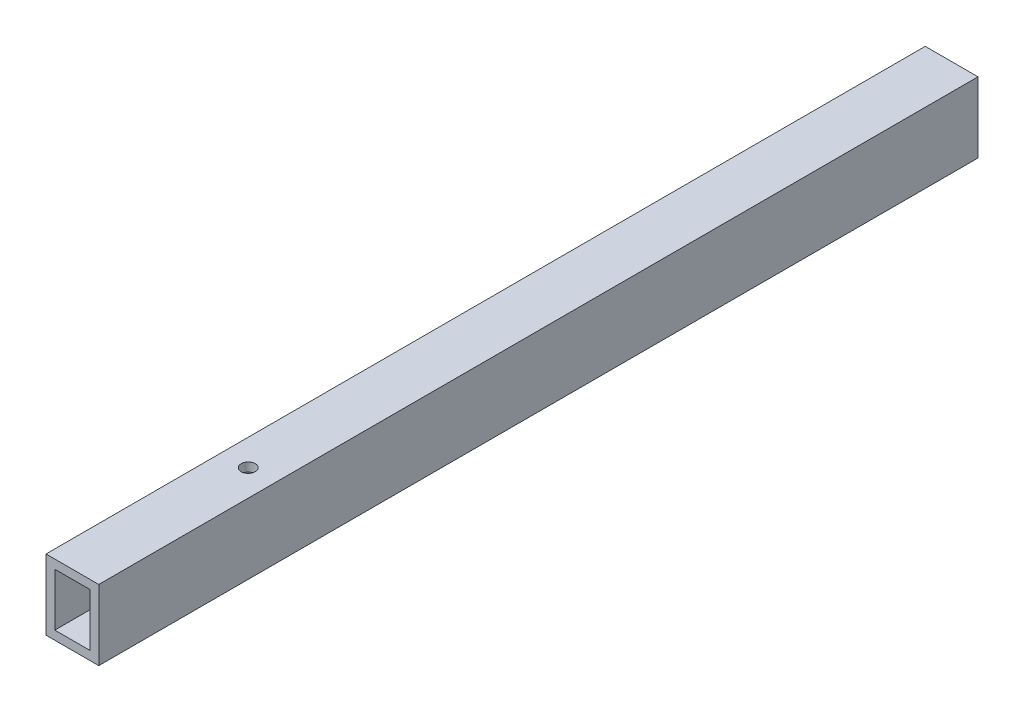
SolidWorks part; units mm, degrees
ref_plane "Plan de face" through (0, 0, 0) normal (0, 0, 1) x (1, 0, 0)
ref_plane "Plan de dessus" through (0, 0, 0) normal (0, 1, 0) x (1, 0, 0)
ref_plane "Plan de droite" through (0, 0, 0) normal (1, 0, 0) x (0, 0, -1)
sketch "Esquisse1" plane through (0, 0, 0) normal (0, 0, 1) x (1, 0, 0)
  line L1 (0, 0) -> (6, 0)
  line L2 (0, 0) -> (0, 8)
  line L3 (0, 8) -> (6, 8)
  line L4 (6, 0) -> (6, 8)
  dimension "D1" = 6
  dimension "D2" = 8
extrude "Boss.-Extru.1" add sketch "Esquisse1" against normal blind 100
sketch "Esquisse2" plane through (0, 0, 0) normal (0, 0, 1) x (1, 0, 0)
  line L0 (6, 0) -> (6, 8) construction
  line L1 (1, 7) -> (5, 7)
  line L2 (1, 7) -> (1, 1)
  line L3 (1, 1) -> (5, 1)
  line L4 (5, 7) -> (5, 1)
  line L5 (0, 0) -> (6, 0) construction
  dimension "D1" = 4
  dimension "D2" = 6
  dimension "D3" = 1
  dimension "D4" = 1
extrude "Enlèv. mat.-Extru.1" cut sketch "Esquisse2" against normal blind 80
hole_wizard "Trou taraudé M21" positions "Esquisse3" profile "Esquisse4" tap size "M2" standard "ISO"
sketch "Esquisse3" plane through (0, 8, 0) normal (0, 1, 0) x (1, 0, 0)
  line L0 (6, 0) -> (0, 0) construction
  line L1 (0, 100) -> (0, 0) construction
  point P0 (3, 20)
  dimension "D1" = 20
  dimension "D2" = 3
sketch "Esquisse4" plane through (3, 8, -20) normal (1, 0, 0) x (0, 0, 1)
  line L0 (0, 0) -> (0, 4.4807)
  line L1 (0, 4.4807) -> (0.8, 4)
  line L2 (0.8, 4) -> (0.8, 0)
  line L5 (0.8, 0) -> (0, 0)
  line L10 (0, 4.4807) -> (-0.8, 4) construction
  line L11 (0, -6.35) -> (0, 107.95) construction
  dimension "Diamètre du trou pour taraudage" = 1.6
  dimension "Profondeur du trou pour taraudage" = 4
  dimension "Angle de pointe" = 118
cosmetic thread "Filetage de perçage1" parameters "D1"=1, "D2"=2
hole_wizard "Trou taraudé M31" positions "Esquisse5" profile "Esquisse6" tap size "M3" standard "ISO"
sketch "Esquisse5" plane through (0, 0, -100) normal (0, 0, -1) x (-1, 0, 0)
  line L0 (0, 8) -> (0, 0) construction
  line L1 (-6, 8) -> (0, 8) construction
  point P0 (-3, 4)
  dimension "D1" = 3
  dimension "D2" = 4
cosmetic thread "Filetage de perçage2" parameters "D1"=6, "D2"=3
sketch "Esquisse6" plane through (3, 4, -100) normal (1, 0, 0) x (0, 1, 0)
  line L0 (0, 0) -> (0, 10.7511)
  line L1 (0, 10.7511) -> (1.25, 10)
  line L2 (1.25, 10) -> (1.25, 0)
  line L5 (1.25, 0) -> (0, 0)
  line L10 (0, 10.7511) -> (-1.25, 10) construction
  line L11 (0, -6.35) -> (0, 107.95) construction
  dimension "Diamètre du trou pour taraudage" = 2.5
  dimension "Profondeur du trou pour taraudage" = 10
  dimension "Angle de pointe" = 118
